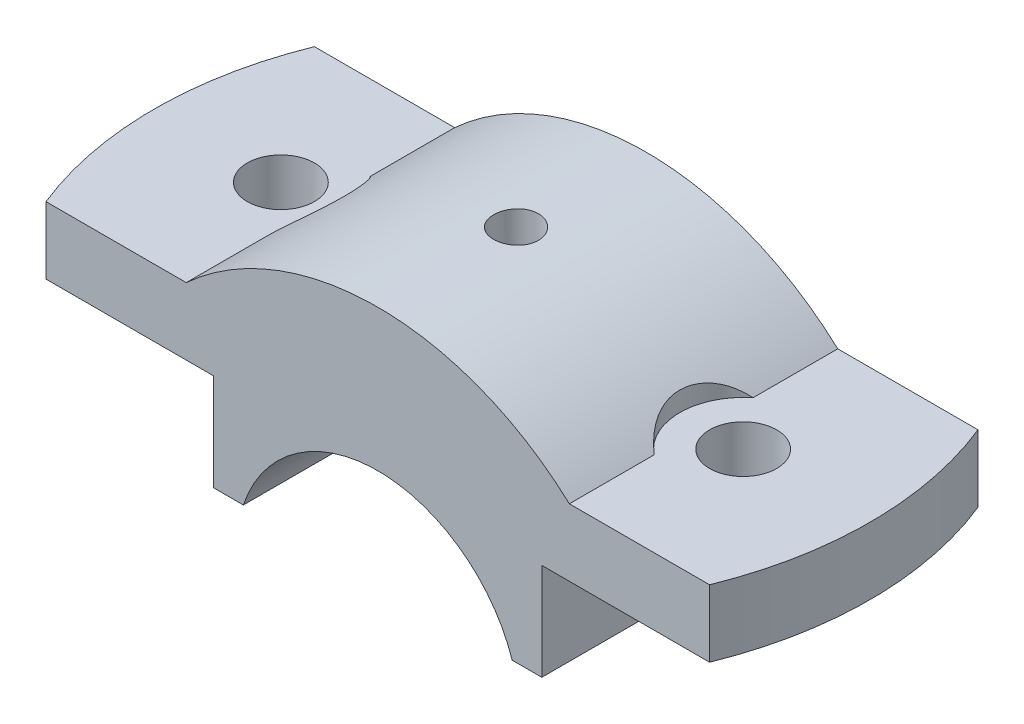
SolidWorks part; units mm, degrees
ref_plane "Front Plane" through (0, 0, 0) normal (0, 0, 1) x (1, 0, 0)
ref_plane "Top Plane" through (0, 0, 0) normal (0, 1, 0) x (1, 0, 0)
ref_plane "Right Plane" through (0, 0, 0) normal (1, 0, 0) x (0, 0, -1)
sketch "Sketch1" plane through (0, 0, 0) normal (0, 0, 1) x (1, 0, 0)
  line L0 (0, 0) -> (0, 67.2511) construction
  line L1 (-18.0278, 6) -> (-22, 6)
  line L2 (-22, 6) -> (-22, 19)
  line L3 (-22, 19) -> (-50, 19)
  line L4 (-50, 19) -> (-50, 28)
  line L5 (-50, 28) -> (-25.6905, 28)
  line L6 (18.0278, 6) -> (22, 6)
  line L7 (22, 6) -> (22, 19)
  line L8 (22, 19) -> (50, 19)
  line L9 (50, 19) -> (50, 28)
  line L10 (50, 28) -> (25.6905, 28)
  arc A0 (-18.0278, 6) -> (18.0278, 6) centre (0, 0) cw
  arc A1 (-25.6905, 28) -> (25.6905, 28) centre (0, 0) cw
  dimension "D1" = 19
  dimension "D4" = 38
  dimension "D2" = 44
  dimension "D3" = 100
  dimension "D5" = 9
  dimension "D6" = 13
  dimension "D7" = 6
extrude "Boss-Extrude1" add sketch "Sketch1" along normal mid plane 36
hole_wizard "Ø8.0mm Dowel Hole1" positions "Sketch3" profile "Sketch2" hole size "Ø8.0" standard "ISO" end condition through all
sketch "Sketch3" plane through (0, 28, 0) normal (0, 1, 0) x (1, 0, 0)
  point P0 (-31, 0)
  dimension "D1" = 31
sketch "Sketch2" plane through (-31, 28, 0) normal (1, 0, 0) x (0, 0, 1)
  line L0 (0, 0) -> (0, 22)
  line L1 (0, 22) -> (4.5, 22)
  line L2 (4.5, 22) -> (4.5, 0)
  line L5 (4.5, 0) -> (0, 0)
  line L11 (0, -6.35) -> (0, 107.95) construction
  dimension "Thru Hole Dia." = 9
  dimension "Thru Hole Depth" = 22
sketch "Sketch6" plane through (0, 28, 0) normal (0, 1, 0) x (1, 0, 0)
  line L0 (-44.4972, 18) -> (-50, 18)
  line L1 (-25.6905, 18) -> (-50, 18) construction
  line L2 (-50, 18) -> (-50, -18)
  line L3 (-50, -18) -> (-44.4972, -18)
  line L4 (44.4972, 18) -> (50, 18)
  line L5 (50, 18) -> (25.6905, 18) construction
  line L6 (50, 18) -> (50, -18)
  line L7 (50, -18) -> (44.4972, -18)
  line L8 (50, -18) -> (25.6905, -18) construction
  arc A0 (-44.4972, 18) -> (-44.4972, -18) centre (0, 0) ccw
  arc A1 (44.4972, -18) -> (44.4972, 18) centre (0, 0) ccw
  dimension "D1" = 96
extrude "Cut-Extrude3" cut sketch "Sketch6" against normal blind 35 contours A0 L1 L2 L3 | A0 L7 L6 L4
sketch "Sketch9" plane through (0, 28, 0) normal (0, 1, 0) x (1, 0, 0)
  line L0 (-25.6905, -18) -> (-25.6905, 18) construction
  line L1 (-25.6905, 6.6377) -> (-25.6905, -6.6377)
  arc A0 (-25.6905, 6.6377) -> (-25.6905, -6.6377) centre (-31, 0) cw
  dimension "D1" = 8.5
extrude "Cut-Extrude4" cut sketch "Sketch9" along normal blind 3
mirror "Mirror3" about plane through (0, 0, 0) normal (1, 0, 0) of "Cut-Extrude4"
mirror "Mirror4" about plane through (0, 0, 0) normal (1, 0, 0) of "Ø8.0mm Dowel Hole1"
hole_wizard "CBORE for M5 Hex Head Bolt2" positions "3DSketch1" profile "Sketch10" counterbore size "M5" standard "ISO"
sketch3d "3DSketch1"
  point P0 (0, 0, 0)
  point P3 (0, 0, 0)
  point P5 (-0.0901, 37.9999, -0.6308)
sketch "Sketch10" plane through (-0.0901, 37.9999, -0.6308) normal (0, 0, 1) x (-1, -0.0024, 0)
  line L0 (0, 0) -> (0, 32.1138)
  line L1 (0, 32.1138) -> (2.5, 32.1138)
  line L2 (2.5, 13.3001) -> (2.5, 32.1138)
  line L3 (2.5, 13.3001) -> (2.9995, 13)
  line L4 (2.9995, 13) -> (3, 13)
  line L5 (3, 13) -> (3, 0)
  line L7 (0, 0) -> (3, 0)
  line L9 (-2.5, 13.3001) -> (-2.9995, 13) construction
  line L11 (0, -6.35) -> (0, 107.95) construction
  dimension "Thru Hole Dia." = 5
  dimension "Thru Hole Depth" = 32.1138
  dimension "C'Bore Dia." = 6
  dimension "C'Bore Depth" = 13
  dimension "Mid C'Sink Dia." = 5.999
  dimension "Mid C'Sink Angle" = 118
